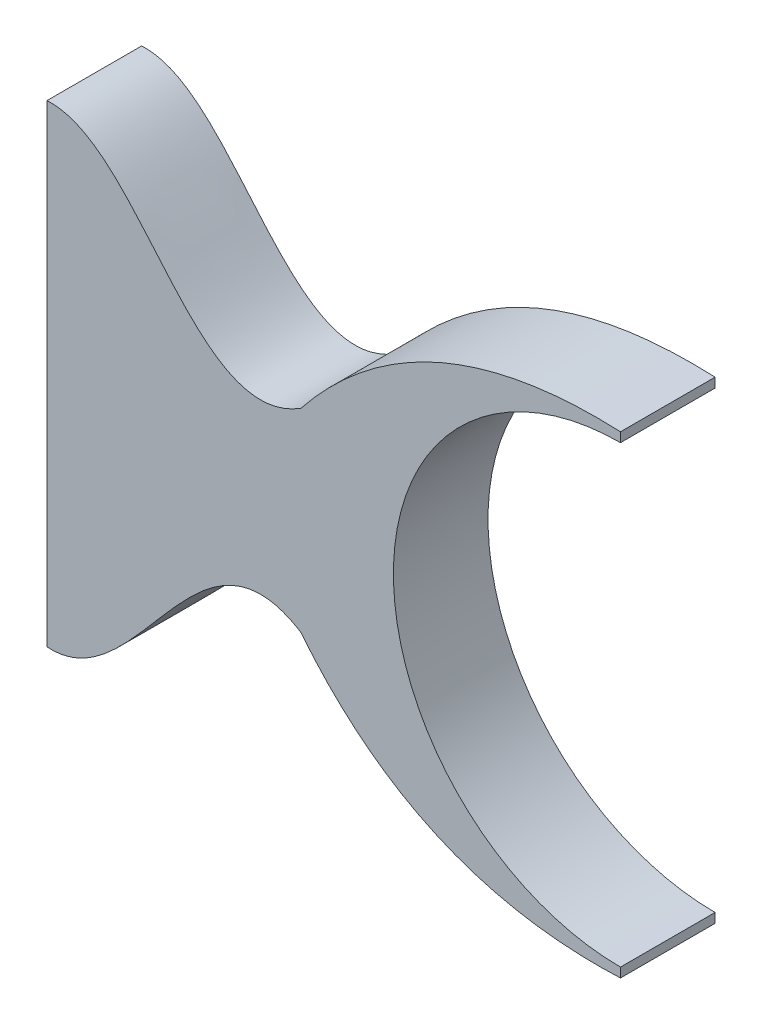
SolidWorks part; units mm, degrees
ref_plane "Front Plane" through (0, 0, 0) normal (0, 0, 1) x (1, 0, 0)
ref_plane "Top Plane" through (0, 0, 0) normal (0, 1, 0) x (1, 0, 0)
ref_plane "Right Plane" through (0, 0, 0) normal (1, 0, 0) x (0, 0, -1)
sketch "Sketch1" plane through (0, 0, 0) normal (0, 0, 1) x (1, 0, 0)
  line L0 (0, 0) -> (-9.9188, 0) construction
  line L1 (-6.0626, 2.5) -> (-6.0626, -2.5)
  line L2 (0, 2.5) -> (0, 2.4)
  line L3 (0, -2.5) -> (0, -2.4)
  arc A1 (0, 2.4) -> (0, -2.4) centre (0, 0) ccw
  spline S0 degree 2 poles (0, 2.5) (-2.1284, 2.5961) (-3.3783, 1.0256) knots 0 0 0 1 1 1
  spline S1 degree 3 poles (-3.3783, 1.0256) (-4.4922, 0.3252) (-5.0825, 2.5685) (-6.0626, 2.5) knots 0 0 0 0 1 1 1 1
  spline S2 degree 3 poles (-3.3783, -1.0256) (-4.4922, -0.3252) (-5.0825, -2.5685) (-6.0626, -2.5) knots 0 0 0 0 1 1 1 1
  spline S3 degree 2 poles (0, -2.5) (-2.1284, -2.5961) (-3.3783, -1.0256) knots 0 0 0 1 1 1
  dimension "D2" = 4.8
extrude "Boss-Extrude1" add sketch "Sketch1" along normal blind 1
